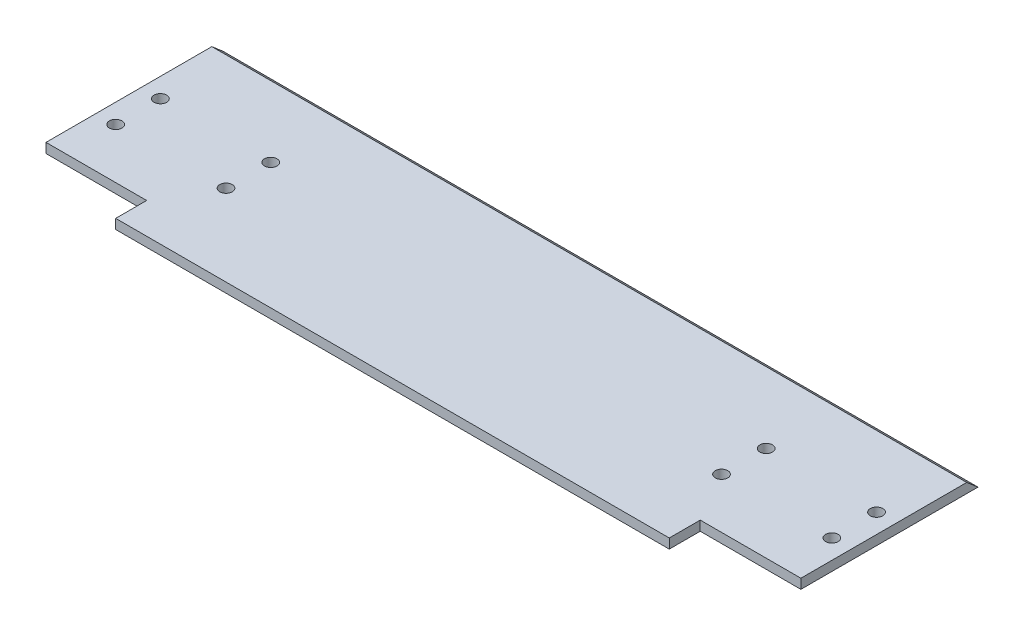
SolidWorks part; units mm, degrees
ref_plane "Alzado" through (0, 0, 0) normal (0, 0, 1) x (1, 0, 0)
ref_plane "Planta" through (0, 0, 0) normal (0, 1, 0) x (1, 0, 0)
ref_plane "Vista lateral" through (0, 0, 0) normal (1, 0, 0) x (0, 0, -1)
sketch "Croquis1" plane through (0, 0, 0) normal (0, 1, 0) x (1, 0, 0)
  line L0 (0, 0) -> (0, -39.0138) construction
  line L1 (0, 0) -> (32.7523, 0) construction
  line L2 (-71.5, -87) -> (71.5, -87)
  line L3 (71.5, -87) -> (71.5, -25)
  line L4 (97.5, 0) -> (97.5, 1)
  line L5 (97.5, 1) -> (97.5, 5.7)
  line L6 (45, 5.7) -> (-45, 5.7)
  line L7 (71.5, -25) -> (97.5, -25)
  line L8 (97.5, -25) -> (97.5, 0)
  line L9 (97.5, 5.7) -> (45, 5.7)
  line L10 (-97.5, 0) -> (-97.5, 1)
  line L11 (-97.5, -25) -> (-97.5, 0)
  line L12 (-71.5, -25) -> (-97.5, -25)
  line L13 (-71.5, -87) -> (-71.5, -25)
  line L14 (102.2367, -56) -> (23.0863, -56) construction
  line L15 (-71.5, -61) -> (71.5, -61)
  line L16 (64, -12) -> (64, -0.46) construction
  line L19 (-97.5, 1) -> (-97.5, 5.7)
  line L20 (-97.5, 5.7) -> (-45, 5.7)
  circle A0 centre (64, -12) radius 1.625
  circle A1 centre (92.5, -12) radius 1.625
  circle A2 centre (-92.5, -12) radius 1.625
  circle A3 centre (64, -0.46) radius 1.625
  circle A4 centre (92.5, -0.46) radius 1.625
  circle A5 centre (-92.5, -0.46) radius 1.625
  circle A6 centre (-64, -0.46) radius 1.625
  circle A7 centre (-64, -12) radius 1.625
  point P13 (0, 5.7)
  point P18 (0, -87)
  point P41 (0, 62)
  point P42 (0, 75)
  dimension "D10" = 3.25
  dimension "D12" = 5
  dimension "D1" = 45
  dimension "D3" = 62
  dimension "D4" = 4.7
  dimension "D5" = 1
  dimension "D6" = 25
  dimension "D7" = 26
  dimension "D8" = 71.5
  dimension "D9" = 44
  dimension "D11" = 7.5
  dimension "D13" = 28.5
  dimension "D14" = 2
  dimension "D15" = 11.54
  dimension "D25" = 97.5
  dimension "D26" = 31
extrude "Cuerpo Inicial" add sketch "Croquis1" along normal blind 2.5
sketch "Croquis3" plane through (97.5, 0, 0) normal (1, 0, 0) x (0, 0, -1)
  line L0 (5.7, 2.5) -> (17.8332, 2.5)
  line L1 (17.8332, 2.5) -> (20.75, 0)
  line L2 (20.75, 0) -> (5.7, 0)
  line L3 (5.7, 0) -> (5.7, 2.5)
  dimension "D1" = 40.6
  dimension "D2" = 15.05
extrude "Saliente-Extruir2" add sketch "Croquis3" against normal up to surface (195 mm away) up to face at (-97.5, 1.25, 9.65)
sketch "Croquis6" plane through (0, 2.5, 0) normal (0, 1, 0) x (1, 0, 0)
  line L0 (-71.5, -61) -> (-71.5, -25) construction
  line L1 (-71.5, -33) -> (71.5, -33)
  line L2 (-71.5, -33) -> (-71.5, -61)
  line L3 (-71.5, -61) -> (71.5, -61)
  line L4 (71.5, -33) -> (71.5, -61)
  line L5 (-71.5, -61) -> (71.5, -61) construction
  line L6 (71.5, -61) -> (71.5, -25) construction
  circle A0 centre (64, -12) radius 1.625 construction
  dimension "D1" = 21
extrude "Cortar-Extruir1" cut sketch "Croquis6" against normal blind 10
